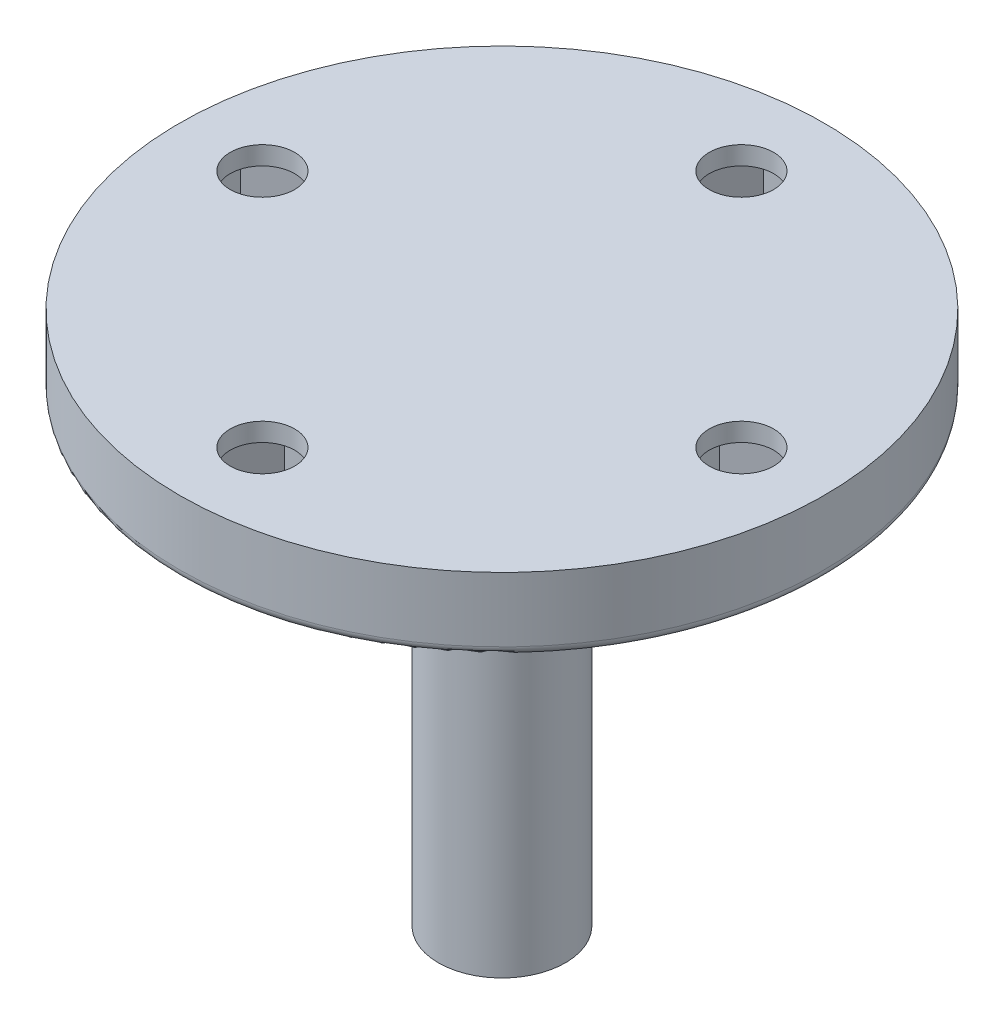
SolidWorks part; units mm, degrees
ref_plane "Спереди" through (0, 0, 0) normal (0, 0, 1) x (1, 0, 0)
ref_plane "Сверху" through (0, 0, 0) normal (0, 1, 0) x (1, 0, 0)
ref_plane "Справа" through (0, 0, 0) normal (1, 0, 0) x (0, 0, -1)
sketch "Эскиз1" plane through (0, 0, 0) normal (0, 1, 0) x (1, 0, 0)
  circle A0 centre (0, 0) radius 3.45
  dimension "D1" = 6.9
extrude "Бобышка-Вытянуть1" add sketch "Эскиз1" along normal blind 23
sketch "Эскиз2" plane through (0, 0, 0) normal (0, -1, 0) x (1, 0, 0)
  line L0 (0, 3.45) -> (0, -3.45) construction
  line L1 (-1.55, 2.3917) -> (-1.55, -2.3917)
  line L2 (1.55, 2.3917) -> (1.55, -2.3917)
  circle A0 centre (0, 0) radius 3.45 construction
  arc A1 (-1.55, -2.3917) -> (1.55, -2.3917) centre (0, 0) ccw
  arc A2 (1.55, 2.3917) -> (-1.55, 2.3917) centre (0, 0) ccw
  point P12 (-1.55, 0)
  point P13 (1.55, 0)
  dimension "D1" = 5.7
  dimension "D2" = 1.55
  dimension "D3" = 1.55
extrude "Вырез-Вытянуть1" cut sketch "Эскиз2" against normal blind 5.5
sketch "Эскиз3" plane through (0, 23, 0) normal (0, 1, 0) x (1, 0, 0)
  circle A0 centre (0, 0) radius 4
  dimension "D1" = 8
extrude "Бобышка-Вытянуть2" add sketch "Эскиз3" along normal blind 2
sketch "Эскиз4" plane through (0, 25, 0) normal (0, 1, 0) x (1, 0, 0)
  circle A0 centre (0, 0) radius 17.5
  dimension "D1" = 35
extrude "Бобышка-Вытянуть3" add sketch "Эскиз4" along normal blind 4
sketch "Эскиз5" plane through (0, 25, 0) normal (0, -1, 0) x (1, 0, 0)
  line L0 (0, 17.5) -> (0, -17.5) construction
  line L1 (-17.5, 0) -> (17.5, 0) construction
  line L2 (13, -3.2793) -> (15.84, -1.6397)
  line L3 (3.2793, 13) -> (1.6397, 15.84)
  line L4 (1.6397, 15.84) -> (-1.6397, 15.84)
  line L5 (-1.6397, 15.84) -> (-3.2793, 13)
  line L6 (-3.2793, 13) -> (-1.6397, 10.16)
  line L7 (-1.6397, 10.16) -> (1.6397, 10.16)
  line L8 (1.6397, 10.16) -> (3.2793, 13)
  line L9 (9.25, -9.25) -> (-9.25, -9.25) construction
  line L10 (9.25, -9.25) -> (9.25, 9.25) construction
  line L11 (9.25, 9.25) -> (-9.25, 9.25) construction
  line L12 (-9.25, -9.25) -> (-9.25, 9.25) construction
  line L13 (9.25, -9.25) -> (-9.25, 9.25) construction
  line L14 (9.25, 9.25) -> (-9.25, -9.25) construction
  line L15 (15.84, -1.6397) -> (15.84, 1.6397)
  line L16 (15.84, 1.6397) -> (13, 3.2793)
  line L17 (13, 3.2793) -> (10.16, 1.6397)
  line L18 (10.16, 1.6397) -> (10.16, -1.6397)
  line L19 (10.16, -1.6397) -> (13, -3.2793)
  line L20 (-3.2793, -13) -> (-1.6397, -15.84)
  line L21 (-1.6397, -15.84) -> (1.6397, -15.84)
  line L22 (1.6397, -15.84) -> (3.2793, -13)
  line L23 (3.2793, -13) -> (1.6397, -10.16)
  line L24 (1.6397, -10.16) -> (-1.6397, -10.16)
  line L25 (-1.6397, -10.16) -> (-3.2793, -13)
  line L26 (-13, 3.2793) -> (-15.84, 1.6397)
  line L27 (-15.84, 1.6397) -> (-15.84, -1.6397)
  line L28 (-15.84, -1.6397) -> (-13, -3.2793)
  line L29 (-13, -3.2793) -> (-10.16, -1.6397)
  line L30 (-10.16, -1.6397) -> (-10.16, 1.6397)
  line L31 (-10.16, 1.6397) -> (-13, 3.2793)
  circle A0 centre (0, 0) radius 17.5 construction
  circle A1 centre (0, 13) radius 2.84 construction
  circle A2 centre (13, 0) radius 2.84 construction
  circle A3 centre (0, -13) radius 2.84 construction
  circle A4 centre (-13, 0) radius 2.84 construction
  point P8 (0, 0)
  point P48 (0, 0)
  dimension "D1" = 18.5
  dimension "D2" = 18.5
  dimension "D3" = 13
  dimension "D4" = 4
extrude "Вырез-Вытянуть2" cut sketch "Эскиз5" against normal blind 3
sketch "Эскиз6" plane through (0, 28, 0) normal (0, -1, 0) x (1, 0, 0)
  line L0 (0, 17.5) -> (0, -18.0329) construction
  circle A0 centre (0, 0) radius 17.5 construction
  circle A1 centre (0, 13) radius 1.75
  circle A2 centre (13, 0) radius 1.75
  circle A3 centre (0, -13) radius 1.75
  circle A4 centre (-13, 0) radius 1.75
  point P17 (0, 0)
  dimension "D1" = 3.5
  dimension "D2" = 4
extrude "Вырез-Вытянуть3" cut sketch "Эскиз6" against normal through all
fillet "Скругление1" radius 0.5 1 edges at (0, 25, 17.5)
fillet "Скругление2" radius 1 1 edges at (0, 25, 4)
